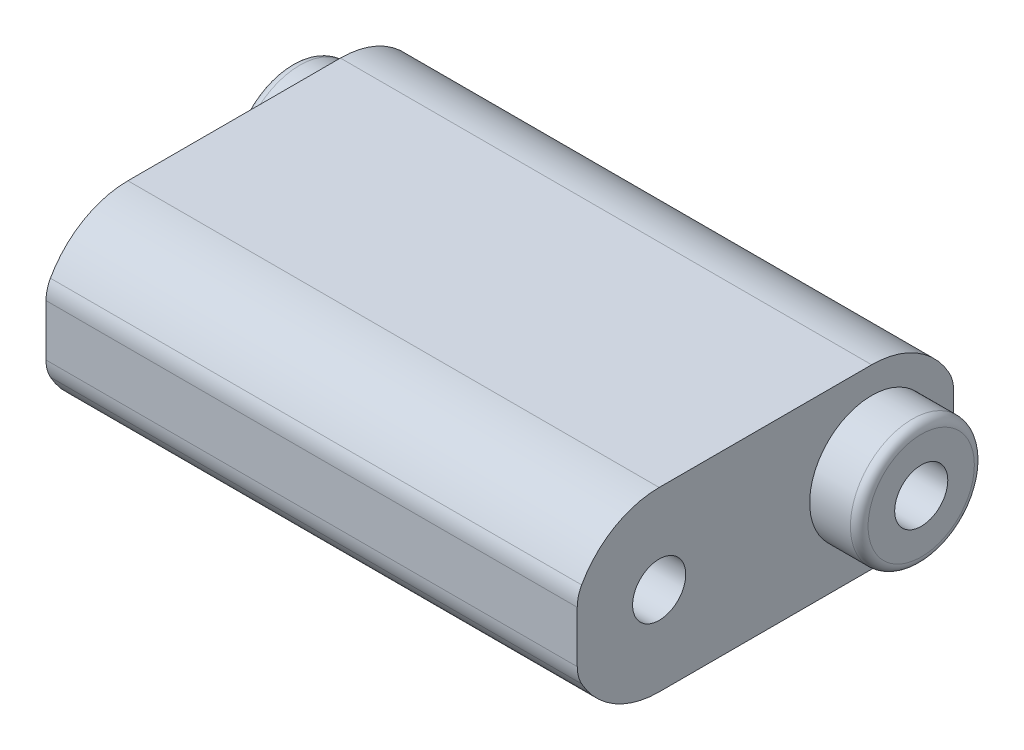
SolidWorks part; units mm, degrees
material "6061 合金"
ref_plane "前视基准面" through (0, 0, 0) normal (0, 0, 1) x (1, 0, 0)
ref_plane "上视基准面" through (0, 0, 0) normal (0, 1, 0) x (1, 0, 0)
ref_plane "右视基准面" through (0, 0, 0) normal (1, 0, 0) x (0, 0, -1)
sketch "草图2" plane through (0, 0, 0) normal (1, 0, 0) x (0, 0, -1)
  line L0 (106.2493, 19) -> (106.2493, -19)
  line L1 (60, 50) -> (-60, 50)
  line L2 (60, 50) -> (60, -50)
  line L3 (60, -50) -> (-60, -50)
  line L4 (-60, 50) -> (-60, -50)
  line L5 (60, 50) -> (-60, -50) construction
  line L6 (60, -50) -> (-60, 50) construction
  line L7 (0, 55) -> (0, -55) construction
  line L8 (-106.2493, 19) -> (-106.2493, -19)
  arc A0 (106.2493, 19) -> (106.2493, -19) centre (60, 0) ccw
  arc A1 (-106.2493, -19) -> (-106.2493, 19) centre (-60, 0) ccw
  arc A2 (106.2493, -19) -> (106.2493, 19) centre (60, 0) ccw construction
  arc A3 (-106.2493, 19) -> (-106.2493, -19) centre (-60, 0) ccw construction
  point P0 (0, 0)
  dimension "D3" = 0
  dimension "D1" = 100
  dimension "D2" = 120
  dimension "D4" = 38
extrude "凸台-拉伸1" add sketch "草图2" along normal blind 300 contours L4 A1 | L4 A1 | A1 L3 A0 L1 | L2 A0 | L2 A0
sketch "草图3" plane through (0, 0, 0) normal (-1, 0, 0) x (0, 0, 1)
  circle A0 centre (60, 0) radius 15
  circle A2 centre (-60, 0) radius 15
  dimension "D1" = 30
  dimension "D2" = 30
extrude "切除-拉伸1" cut sketch "草图3" against normal blind 300
sketch "草图4" plane through (0, 0, 0) normal (-1, 0, 0) x (0, 0, 1)
  circle A1 centre (-60, 0) radius 15
  circle A2 centre (-60, 0) radius 35
  dimension "D1" = 70
extrude "凸台-拉伸2" add sketch "草图4" along normal blind 28
sketch "草图6" plane through (300, 0, 0) normal (1, 0, 0) x (0, 0, -1)
  circle A6 centre (60, 0) radius 15
  circle A7 centre (60, 0) radius 35
  dimension "D1" = 70
extrude "凸台-拉伸3" add sketch "草图6" along normal blind 28
fillet "圆角2" radius 5 2 edges at (-28, 0, -25) (328, 0, -95)
fillet "圆角3" radius 20 4 edges at (150, -19, 106.2493) (150, 19, 106.2493) (150, 19, -106.2493) (150, -19, -106.2493)
ref_point "点1"
